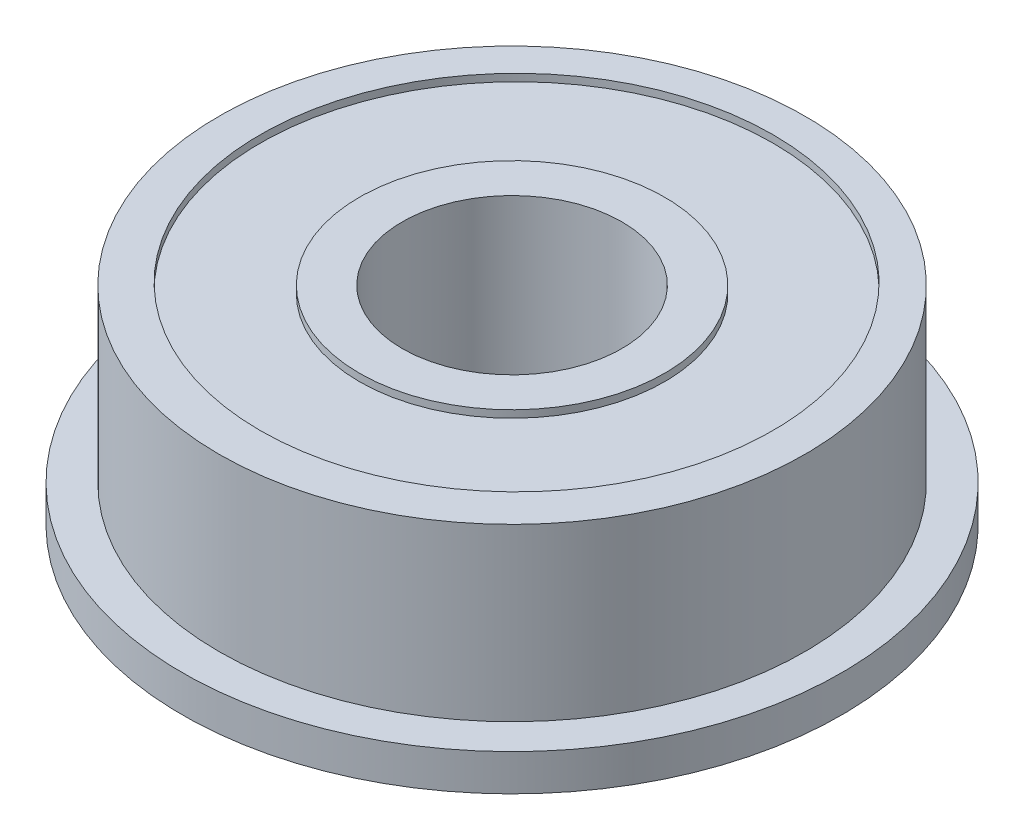
SolidWorks part; units mm, degrees
ref_plane "前视基准面" through (0, 0, 0) normal (0, 0, 1) x (1, 0, 0)
ref_plane "上视基准面" through (0, 0, 0) normal (0, 1, 0) x (1, 0, 0)
ref_plane "右视基准面" through (0, 0, 0) normal (1, 0, 0) x (0, 0, -1)
sketch "草图1" plane through (0, 0, 0) normal (0, 1, 0) x (1, 0, 0)
  circle A0 centre (0, 0) radius 4.5
  circle A1 centre (0, 0) radius 12
  dimension "D1" = 9
  dimension "D2" = 24
extrude "凸台-拉伸1" add sketch "草图1" along normal blind 7
sketch "草图2" plane through (0, 0, 0) normal (0, -1, 0) x (1, 0, 0)
  circle A0 centre (0, 0) radius 4.5 construction
  circle A1 centre (0, 0) radius 4.5
  circle A2 centre (0, 0) radius 13.5
  dimension "D1" = 27
extrude "凸台-拉伸2" add sketch "草图2" along normal blind 1.5
sketch "草图3" plane through (0, 7, 0) normal (0, 1, 0) x (1, 0, 0)
  circle A0 centre (0, 0) radius 6.25
  circle A1 centre (0, 0.1856) radius 10.5
  dimension "D1" = 12.5
  dimension "D2" = 21
extrude "切除-拉伸1" cut sketch "草图3" against normal blind 0.3
sketch "草图4" plane through (0, -1.5, 0) normal (0, -1, 0) x (1, 0, 0)
  circle A0 centre (0, 0) radius 6.25
  circle A1 centre (0, 0) radius 10.5
  dimension "D1" = 12.5
  dimension "D2" = 21
extrude "切除-拉伸2" cut sketch "草图4" against normal blind 0.3
